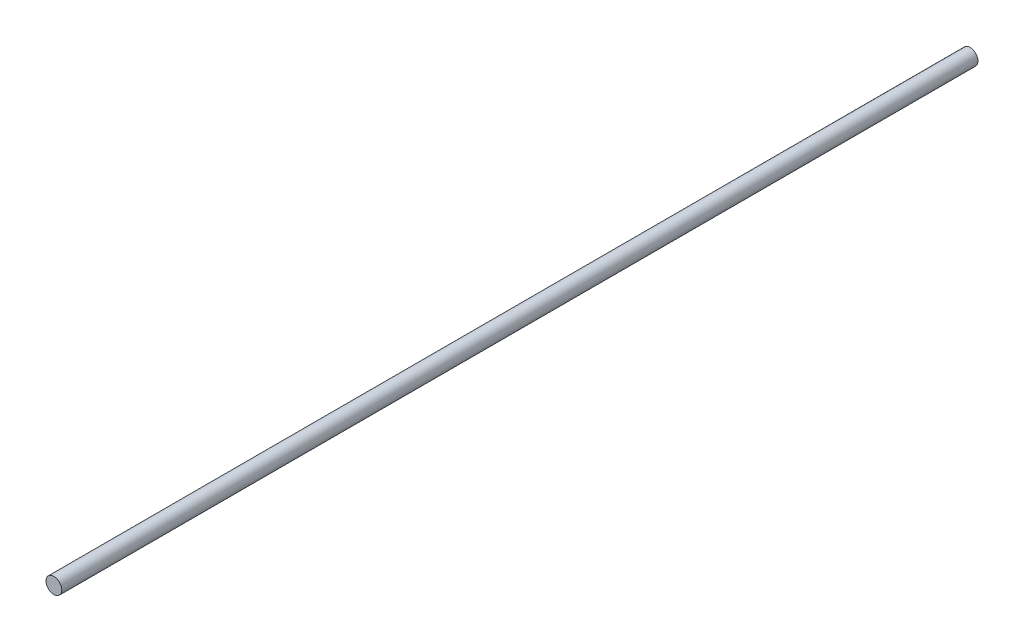
SolidWorks part; units mm, degrees
ref_plane "Plan de face" through (0, 0, 0) normal (0, 0, 1) x (1, 0, 0)
ref_plane "Plan de dessus" through (0, 0, 0) normal (0, 1, 0) x (1, 0, 0)
ref_plane "Plan de droite" through (0, 0, 0) normal (1, 0, 0) x (0, 0, -1)
sketch "Esquisse1" plane through (0, 0, 0) normal (0, 0, 1) x (1, 0, 0)
  circle A0 centre (0, 0) radius 5
  dimension "D1" = 10
extrude "Boss.-Extru.1" add sketch "Esquisse1" along normal blind 580
